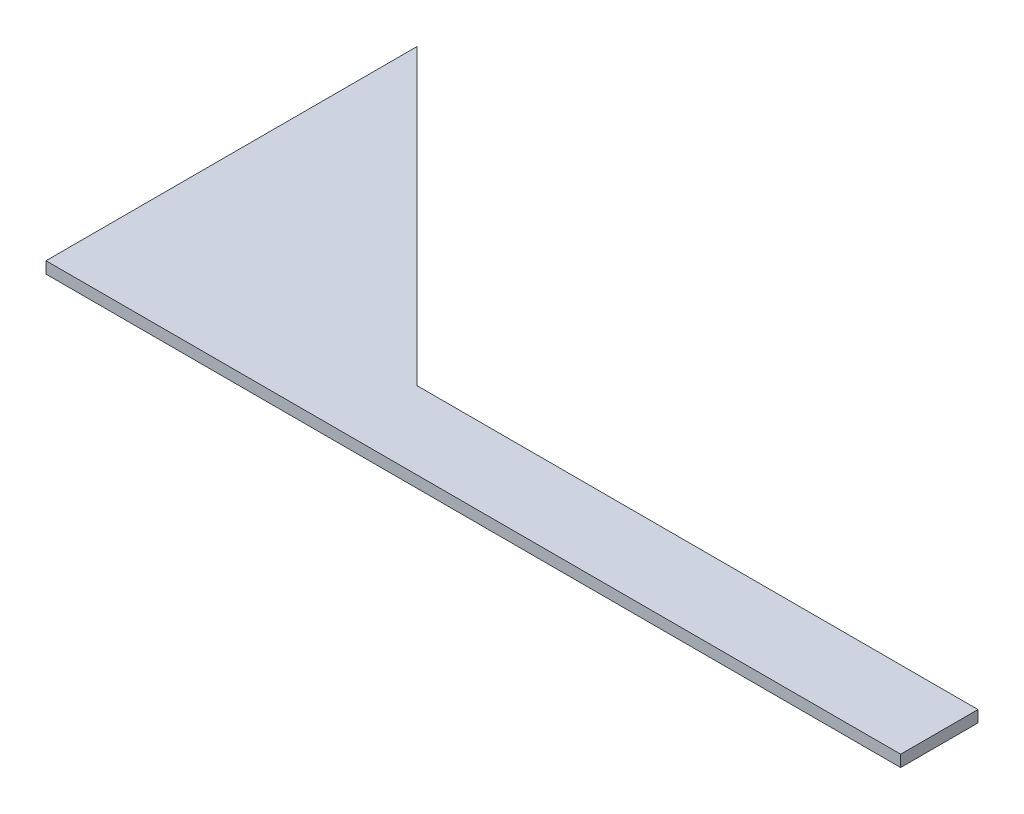
SolidWorks part; units mm, degrees
material "ASTM A36 Steel"
ref_plane "Front Plane" through (0, 0, 0) normal (0, 0, 1) x (1, 0, 0)
ref_plane "Top Plane" through (0, 0, 0) normal (0, 1, 0) x (1, 0, 0)
ref_plane "Right Plane" through (0, 0, 0) normal (1, 0, 0) x (0, 0, -1)
sketch "Sketch1" plane through (0, 0, 0) normal (0, 1, 0) x (1, 0, 0)
  line L0 (0, 0) -> (0, 152.4)
  line L1 (0, 152.4) -> (152.4, 0)
  line L2 (152.4, 0) -> (0, 0)
  line L3 (120.65, 31.75) -> (350.901, 31.75)
  line L4 (350.901, 31.75) -> (350.901, 0)
  line L5 (350.901, 0) -> (152.4, 0)
  dimension "D1" = 152.4
  dimension "D2" = 152.4
  dimension "D3" = 350.901
  dimension "D4" = 31.75
extrude "Boss-Extrude1" add sketch "Sketch1" along normal blind 4.7625 contours L2 L1 L0 | L5 L4 L3 L1
